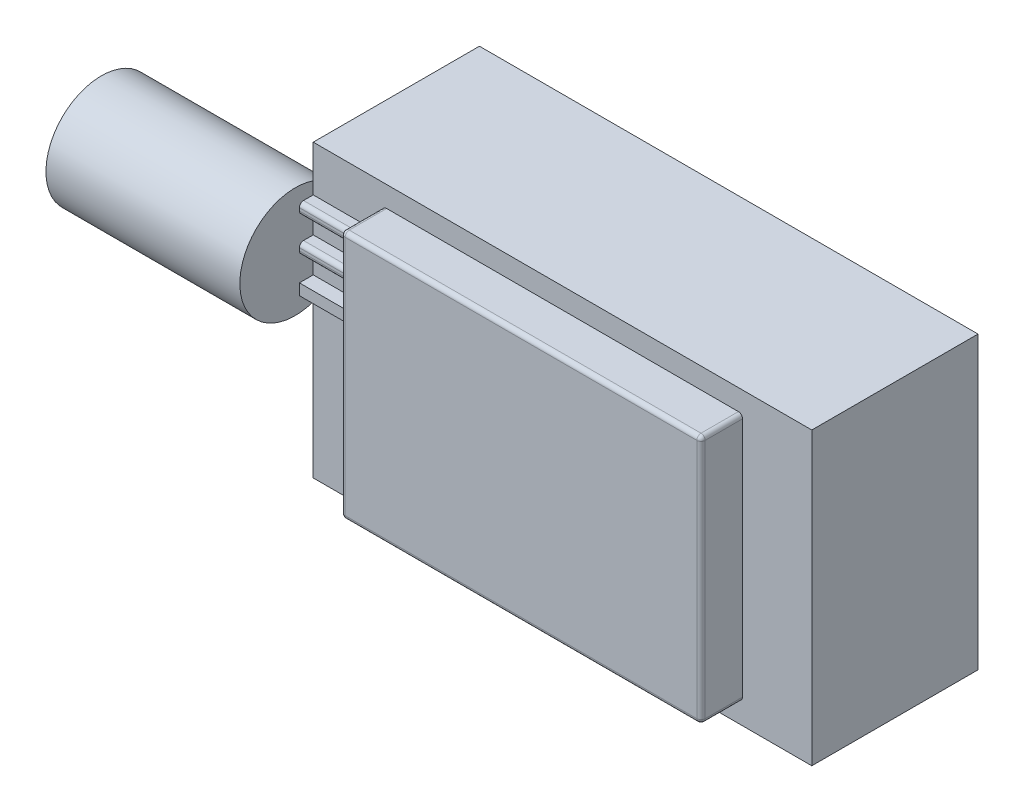
SolidWorks part; units mm, degrees
ref_plane "Přední rovina" through (0, 0, 0) normal (0, 0, 1) x (1, 0, 0)
ref_plane "Horní rovina" through (0, 0, 0) normal (0, 1, 0) x (1, 0, 0)
ref_plane "Pravá rovina" through (0, 0, 0) normal (1, 0, 0) x (0, 0, -1)
sketch "Skica1" plane through (0, 0, 0) normal (0, 0, 1) x (1, 0, 0)
  line L1 (-18, 10.5) -> (18, 10.5)
  line L2 (-18, 10.5) -> (-18, -10.5)
  line L3 (-18, -10.5) -> (18, -10.5)
  line L4 (18, 10.5) -> (18, -10.5)
  line L5 (-18, 10.5) -> (18, -10.5) construction
  line L6 (-18, -10.5) -> (18, 10.5) construction
  point P0 (0, 0)
  dimension "D1" = 21
  dimension "D2" = 36
extrude "Přidat vysunutím1" add sketch "Skica1" along normal blind 15
sketch "Skica2" plane through (0, 0, 15) normal (0, 0, 1) x (1, 0, 0)
  line L1 (-13, 9) -> (13, 9)
  line L2 (-13, 9) -> (-13, -9)
  line L3 (-13, -9) -> (13, -9)
  line L4 (13, 9) -> (13, -9)
  line L5 (-13, 9) -> (13, -9) construction
  line L6 (-13, -9) -> (13, 9) construction
  line L7 (-20.0625, 12.7376) -> (20.0625, 12.7376)
  line L8 (-20.0625, 12.7376) -> (-20.0625, -12.7376)
  line L9 (-20.0625, -12.7376) -> (20.0625, -12.7376)
  line L10 (20.0625, 12.7376) -> (20.0625, -12.7376)
  line L11 (-20.0625, 12.7376) -> (20.0625, -12.7376) construction
  line L12 (-20.0625, -12.7376) -> (20.0625, 12.7376) construction
  point P0 (0, 0)
  point P6 (0, 0)
  dimension "D1" = 26
  dimension "D2" = 18
extrude "Odebrat vysunutím1" cut sketch "Skica2" against normal blind 3
sketch "Skica3" plane through (-18, 0, 0) normal (-1, 0, 0) x (0, 0, 1)
  line L0 (12, 10.5) -> (12, -10.5) construction
  line L1 (12, 10.5) -> (0, 10.5) construction
  circle A0 centre (13.3, 4.3) radius 4
  point P2 (12.9892, 5.389)
  dimension "D1" = 8
  dimension "D2" = 1.3
  dimension "D3" = 6.2
extrude "Přidat vysunutím2" add sketch "Skica3" along normal blind 14
sketch "Skica4" plane through (0, 0, 12) normal (0, 0, 1) x (1, 0, 0)
  line L0 (-18, 8.0829) -> (-18, 0.5171) construction
  line L1 (-18, 7.2) -> (-13.8804, 7.2)
  line L2 (-18, 7.2) -> (-18, 6.4)
  line L3 (-18, 6.4) -> (-13.8804, 6.4)
  line L4 (-13.8804, 7.2) -> (-13.8804, 6.4)
  line L5 (18, 10.5) -> (-18, 10.5) construction
  line L14 (-18, 3.9) -> (-13.8804, 3.9)
  line L15 (-18, 4.7) -> (-18, 3.9)
  line L16 (-18, 4.7) -> (-13.8804, 4.7)
  line L17 (-13.8804, 4.7) -> (-13.8804, 3.9)
  line L18 (-18, 1.4) -> (-13.8804, 1.4)
  line L19 (-18, 2.2) -> (-18, 1.4)
  line L20 (-18, 2.2) -> (-13.8804, 2.2)
  line L21 (-13.8804, 2.2) -> (-13.8804, 1.4)
  dimension "D1" = 3.3
  dimension "D2" = 0.8
  dimension "D3" = 3
extrude "Přidat vysunutím3" add sketch "Skica4" along normal blind 1
fillet "Zaoblit3" radius 0.3 18 edges at (-13.8804, 4.7, 12.5) (-13.8804, 7.2, 12.5) (-13.8804, 3.9, 12.5) (-15.9402, 3.9, 13) (-13.8804, 4.3, 13) (-15.9402, 4.7, 13) (-13.8804, 6.4, 12.5) (-13.8804, 6.8, 13) (-15.9402, 7.2, 13) (-15.9402, 6.4, 13) (13, 9, 13.5) (0, 9, 15) (-13, 9, 13.5) (13, 0, 15) (13, -9, 13.5) (0, -9, 15) (-13, -9, 13.5) (-13, 0, 15)
